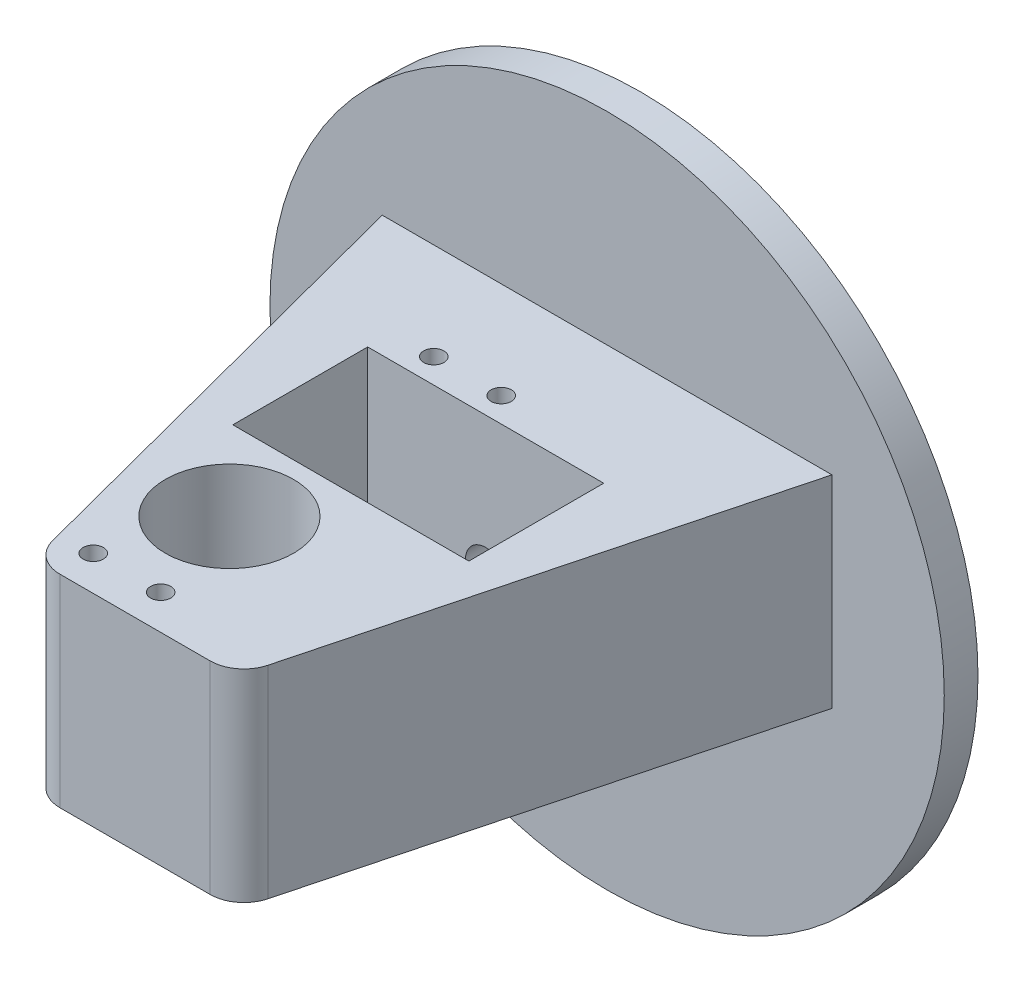
SolidWorks part; units mm, degrees
material "Custom Plastic"
ref_plane "Front Plane" through (0, 0, 0) normal (0, 0, 1) x (1, 0, 0)
ref_plane "Top Plane" through (0, 0, 0) normal (0, 1, 0) x (1, 0, 0)
ref_plane "Right Plane" through (0, 0, 0) normal (1, 0, 0) x (0, 0, -1)
sketch "Sketch1" plane through (0, 0, 0) normal (0, 1, 0) x (1, 0, 0)
  line L0 (-11.1413, 70) -> (11.1413, 70)
  line L11 (15.9781, 66.2674) -> (33.3421, 0)
  line L12 (33.3421, 0) -> (-33.3421, 0)
  line L13 (-33.3421, 0) -> (-15.9781, 66.2674)
  arc A0 (-11.1413, 70) -> (-15.9781, 66.2674) centre (-11.1413, 65) ccw
  arc A1 (11.1413, 70) -> (15.9781, 66.2674) centre (11.1413, 65) cw
  point P12 (-15, 70)
  point P15 (15, 70)
  dimension "D7" = 5
  dimension "D8" = 5
  dimension "D4" = 30
  dimension "D5" = 70
extrude "Boss-Extrude1" add sketch "Sketch1" along normal blind 40
sketch "Sketch9" plane through (0, 0, 0) normal (0, -1, 0) x (1, 0, 0)
  circle A0 centre (-6, -50) radius 9.5
  dimension "D2" = 19
  dimension "D1" = 50
  dimension "D3" = 6
extrude "Cut-Extrude5" cut sketch "Sketch9" against normal blind 20
sketch "Sketch10" plane through (0, 20, 0) normal (0, -1, 0) x (1, 0, 0)
  circle A0 centre (-6, -50) radius 5
  dimension "D1" = 10
extrude "Cut-Extrude6" cut sketch "Sketch10" against normal through all
sketch "Sketch11" plane through (0, 40, 0) normal (0, 1, 0) x (1, 0, 0)
  circle A0 centre (-6, 50) radius 9.5
  dimension "D1" = 19
extrude "Cut-Extrude7" cut sketch "Sketch11" against normal blind 16
scale "Scale1" [suppressed]
sketch "Sketch13" plane through (0, 0, 0) normal (0, -1, 0) x (1, 0, 0)
  line L0 (0, -57.3655) -> (0, -20.9081) construction
  line L1 (-11, -50) -> (32.9469, -50) construction
  line L2 (9.5, -37.5) -> (-9.5, -37.5)
  line L3 (9.5, -37.5) -> (9.5, -62.5)
  line L4 (9.5, -62.5) -> (-9.5, -62.5)
  line L5 (-9.5, -37.5) -> (-9.5, -62.5)
  circle A0 centre (-6, -50) radius 9.5 construction
  circle A1 centre (-6, -50) radius 9.5 construction
  circle A2 centre (-6, -50) radius 5 construction
  dimension "D1" = 19
  dimension "D2" = 25
extrude "Cut-Extrude8" [suppressed] cut sketch "Sketch13" against normal blind 14
sketch "Sketch14" plane through (0, 40, 0) normal (0, 1, 0) x (1, 0, 0)
  line L1 (-17.5, 18) -> (17.5, 18)
  line L2 (-17.5, 18) -> (-17.5, 38)
  line L3 (-17.5, 38) -> (17.5, 38)
  line L4 (17.5, 18) -> (17.5, 38)
  line L5 (-17.5, 18) -> (17.5, 38) construction
  line L6 (-17.5, 38) -> (17.5, 18) construction
  point P0 (0, 28)
  dimension "D1" = 35
  dimension "D2" = 20
extrude "Cut-Extrude9" cut sketch "Sketch14" against normal through all
sketch "Sketch15" plane through (0, 0, 0) normal (0, 0, 1) x (1, 0, 0)
  line L0 (-33.3421, 20) -> (38.5555, 20) construction
  line L1 (-33.3421, 40) -> (-33.3421, 0) construction
  line L2 (0, 0) -> (0, 49.1924) construction
  circle A0 centre (0, 20) radius 3
  dimension "D1" = 6
  dimension "D2" = 0
extrude "Cut-Extrude10" cut sketch "Sketch15" against normal blind 25
sketch "Sketch16" plane through (0, 0, 0) normal (0, 0, 1) x (1, 0, 0)
  line L0 (0, 0) -> (0, 49.9316) construction
  line L1 (-33.3421, 20) -> (71.4669, 20) construction
  line L2 (-33.3421, 40) -> (-33.3421, 0) construction
  circle A0 centre (0, 20) radius 50
  circle A1 centre (0, 20) radius 3
  dimension "D1" = 100
extrude "Boss-Extrude3" add sketch "Sketch16" along normal blind 5
sketch "Sketch17" plane through (0, 40, 0) normal (0, 1, 0) x (1, 0, 0)
  line L1 (-33.3421, 0) -> (35.8642, 0)
  line L2 (-33.3421, 0) -> (-33.3421, 74.867)
  line L3 (-33.3421, 74.867) -> (35.8642, 74.867)
  line L4 (35.8642, 0) -> (35.8642, 74.867)
extrude "Cut-Extrude11" cut sketch "Sketch17" against normal blind 10
sketch "Sketch18" plane through (0, 0, 0) normal (0, -1, 0) x (1, 0, 0)
  circle A0 centre (-1.3502, -64.85) radius 1.5
  circle A1 centre (-11.3502, -64.85) radius 1.5
  dimension "D1" = 3
  dimension "D2" = 64.85
  dimension "D3" = 10
extrude "Cut-Extrude12" cut sketch "Sketch18" against normal blind 10
sketch "Sketch20" plane through (0, 0, 0) normal (0, -1, 0) x (1, 0, 0)
  circle A0 centre (-11.3502, -14.35) radius 1.5
  circle A1 centre (-1.3502, -14.35) radius 1.5
  dimension "D1" = 3
  dimension "D2" = 3
extrude "Cut-Extrude13" cut sketch "Sketch20" against normal blind 10
move or copy body "Body-Move/Copy1" bodies to move or copy 117 copy no rotation origin (0, 20, -32.5) rotation axis (1, 0, 0) rotation angle 180
sketch "Sketch21" plane through (0, 0, -70) normal (0, 0, -1) x (-1, 0, 0)
  point P0 (0, 20)
move or copy body "Body-Move/Copy2" bodies to move or copy 118 copy no translate (0, -20, 70)
